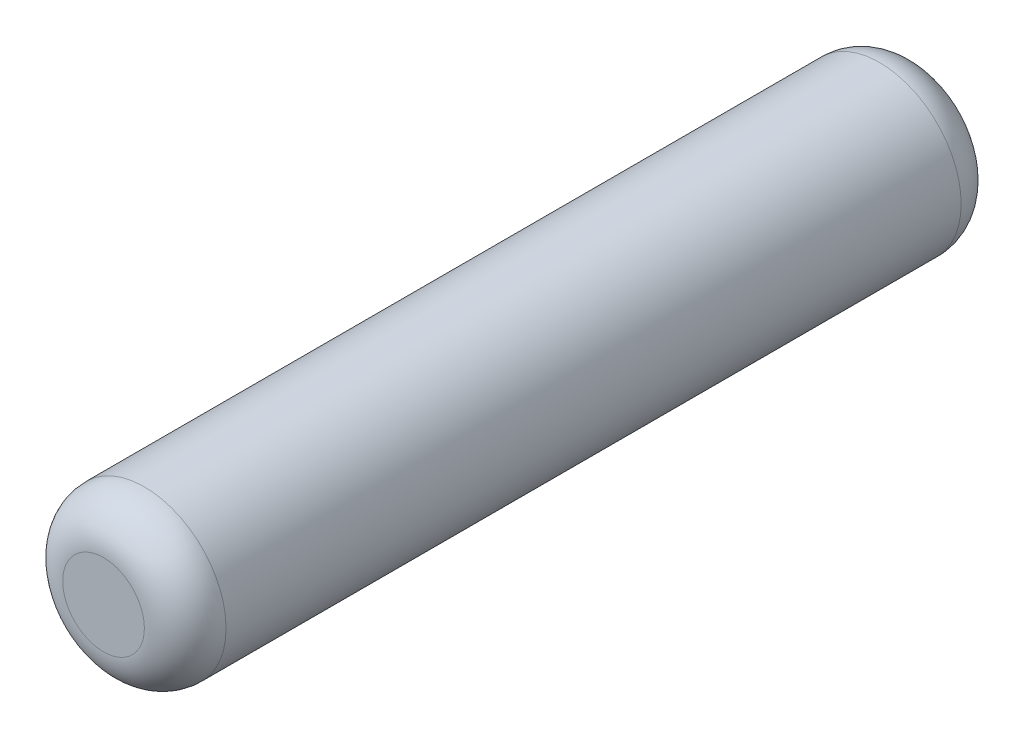
SolidWorks part; units mm, degrees
ref_plane "정면" through (0, 0, 0) normal (0, 0, 1) x (1, 0, 0)
ref_plane "윗면" through (0, 0, 0) normal (0, 1, 0) x (1, 0, 0)
ref_plane "우측면" through (0, 0, 0) normal (1, 0, 0) x (0, 0, -1)
sketch "스케치1" plane through (0, 0, 0) normal (0, 0, 1) x (1, 0, 0)
  circle A0 centre (0, 0) radius 2
  dimension "D1" = 4
extrude "보스-돌출1" add sketch "스케치1" along normal mid plane 20
fillet "필렛1" radius 1 2 edges at (2, 0, -10) (2, 0, 10)
